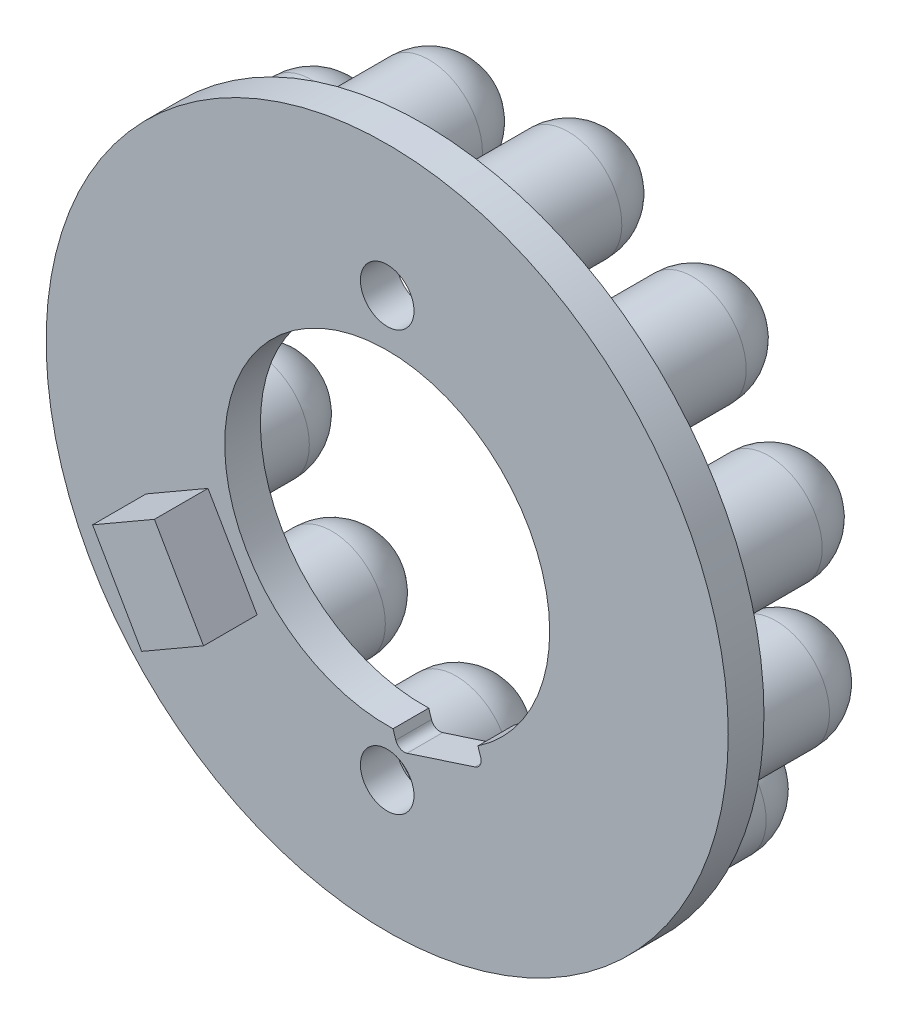
SolidWorks part; units mm, degrees
ref_plane "Front Plane" through (0, 0, 0) normal (0, 0, 1) x (1, 0, 0)
ref_plane "Top Plane" through (0, 0, 0) normal (0, 1, 0) x (1, 0, 0)
ref_plane "Right Plane" through (0, 0, 0) normal (1, 0, 0) x (0, 0, -1)
sketch "Sketch1" plane through (0, 0, 0) normal (0, 0, 1) x (1, 0, 0)
  line L0 (0.3262, -9.0942) -> (0.6352, -10.0452)
  line L1 (0.6352, -10.0452) -> (5.3905, -8.5001)
  line L2 (5.3905, -8.5001) -> (5.0815, -7.5491)
  line L3 (0.3262, -9.0942) -> (5.0815, -7.5491)
  line L4 (0, -11.75) -> (0, 0) construction
  line L5 (0, 0) -> (2.7039, -8.3216) construction
  circle A0 centre (0, 0) radius 9.1
  circle A1 centre (0, 0) radius 19.1
  circle A2 centre (0, -11.75) radius 1.5
  circle A3 centre (0, 11.75) radius 1.5
  circle A4 centre (0, 0) radius 11.75 construction
  dimension "D1" = 38.2
  dimension "D2" = 18.2
  dimension "D3" = 23.5
  dimension "D4" = 3
  dimension "D5" = 5
  dimension "D6" = 1
  dimension "D7" = 18
extrude "Boss-Extrude1" add sketch "Sketch1" along normal blind 2 contours A1 A3 A2 A0 L2 L1 L0
fillet "Fillet1" radius 0.5 2 edges at (0.6352, -10.0452, 1) (5.3905, -8.5001, 1)
sketch "Sketch3" plane through (0, 0, 2) normal (0, 0, 1) x (1, 0, 0)
  line L0 (-10.0353, -2.6184) -> (-13.4994, -4.6184)
  line L1 (-13.4994, -4.6184) -> (-10.7494, -9.3816)
  line L2 (-10.7494, -9.3816) -> (-7.2853, -7.3816)
  line L3 (-7.2853, -7.3816) -> (-10.0353, -2.6184)
  line L4 (0, 0) -> (-8.6603, -5) construction
  line L5 (0, 0) -> (0, 6.3794) construction
  dimension "D1" = 4
  dimension "D2" = 5.5
  dimension "D3" = 10
  dimension "D4" = 120
extrude "Boss-Extrude2" add sketch "Sketch3" along normal blind 3
sketch "Sketch4" plane through (0, 0, 0) normal (0, 0, -1) x (-1, 0, 0)
  line L0 (0, 0) -> (-4.6662, -14.361)
  line L1 (-1.1108, -9.8907) -> (-4.915, -8.6546) construction
  circle A0 centre (-4.6662, -14.361) radius 3
  circle A2 centre (0, 0) radius 18.1 construction
  circle A3 centre (0, 0) radius 19.1 construction
  point P3 (-2.3331, -7.1805)
  point P9 (-3.0129, -9.2727)
  dimension "D1" = 6
  dimension "D2" = 1
extrude "Boss-Extrude3" add sketch "Sketch4" along normal blind 5 contours A0
sketch "Sketch5" plane through (0, 0, -5) normal (0, 0, -1) x (-1, 0, 0)
  line L0 (-4.6662, -11.361) -> (-4.6662, -17.361)
  arc A0 (-4.6662, -17.361) -> (-4.6662, -11.361) centre (-4.6662, -14.361) ccw
  circle A1 centre (-4.6662, -14.361) radius 3 construction
  point P7 (-4.6662, -14.361)
revolve "Revolve1" add sketch "Sketch5" angle 360 about L0
pattern_circular "CirPattern1" count 12 over 360 about axis through (0, 0, 0) along (0, 0, 1) of "Revolve1", "Boss-Extrude3"
